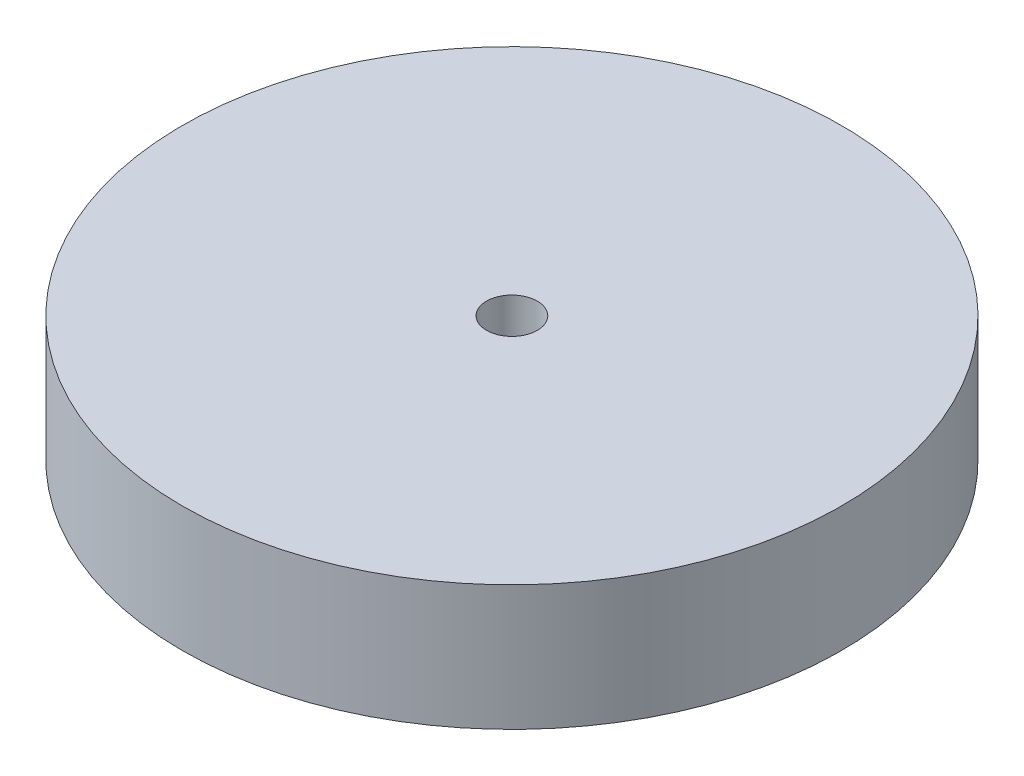
SolidWorks part; units mm, degrees
ref_plane "Front Plane" through (0, 0, 0) normal (0, 0, 1) x (1, 0, 0)
ref_plane "Top Plane" through (0, 0, 0) normal (0, 1, 0) x (1, 0, 0)
ref_plane "Right Plane" through (0, 0, 0) normal (1, 0, 0) x (0, 0, -1)
sketch "Sketch1" plane through (0, 0, 0) normal (0, 1, 0) x (1, 0, 0)
  circle A0 centre (0, 0) radius 50
  dimension "D1" = 100
extrude "Boss-Extrude1" add sketch "Sketch1" along normal blind 19
sketch "Sketch2" plane through (0, 19, 0) normal (0, 1, 0) x (1, 0, 0)
  circle A0 centre (0, 0) radius 3.85
  dimension "D1" = 7.7
extrude "Cut-Extrude2" cut sketch "Sketch2" against normal through all
